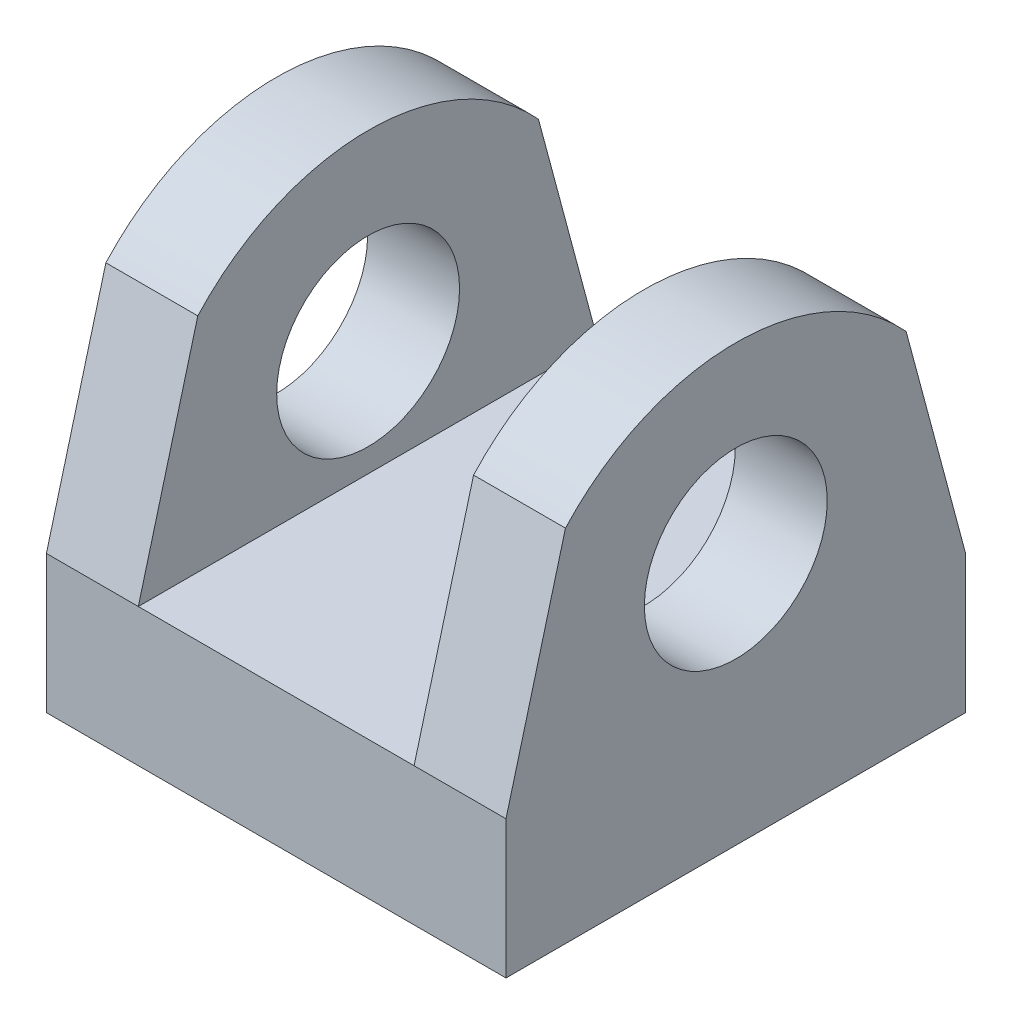
SolidWorks part; units mm, degrees
material "ABS"
ref_plane "Front Plane" through (0, 0, 0) normal (0, 0, 1) x (1, 0, 0)
ref_plane "Top Plane" through (0, 0, 0) normal (0, 1, 0) x (1, 0, 0)
ref_plane "Right Plane" through (0, 0, 0) normal (1, 0, 0) x (0, 0, -1)
sketch "Sketch1" plane through (0, 0, 0) normal (0, 1, 0) x (1, 0, 0)
  line L1 (-12.7, -12.7) -> (12.7, -12.7)
  line L2 (-12.7, -12.7) -> (-12.7, 12.7)
  line L3 (-12.7, 12.7) -> (12.7, 12.7)
  line L4 (12.7, -12.7) -> (12.7, 12.7)
  line L5 (-12.7, -12.7) -> (12.7, 12.7) construction
  line L6 (-12.7, 12.7) -> (12.7, -12.7) construction
  point P0 (0, 0)
  dimension "D1" = 25.4
  dimension "D2" = 25.4
extrude "Boss-Extrude1" add sketch "Sketch1" along normal blind 7.62
sketch "Sketch2" plane through (12.7, 0, 0) normal (1, 0, 0) x (0, 0, -1)
  line L0 (-12.7, 7.62) -> (-9.413, 19.8873)
  line L1 (12.7, 7.62) -> (9.413, 19.8873)
  line L2 (-12.7, 7.62) -> (12.7, 7.62) construction
  line L3 (-12.7, 7.62) -> (12.7, 7.62)
  arc A2 (-9.413, 19.8873) -> (9.413, 19.8873) centre (0, 11.3462) cw
  dimension "D1" = 75
  dimension "D2" = 75
extrude "Boss-Extrude2" add sketch "Sketch2" against normal blind 5.08
ref_plane "Plane1" through (0, 0, 0) normal (1, 0, 0) x (0, 0, -1)
mirror "Mirror1" about plane through (0, 0, 0) normal (1, 0, 0) of "Boss-Extrude2"
sketch "Sketch3" plane through (12.7, 0, 0) normal (1, 0, 0) x (0, 0, -1)
  line L0 (-12.7, 0) -> (12.7, 0) construction
  circle A0 centre (0, 13.97) radius 5.0532
  dimension "D1" = 13.97
extrude "Cut-Extrude1" cut sketch "Sketch3" against normal through all
